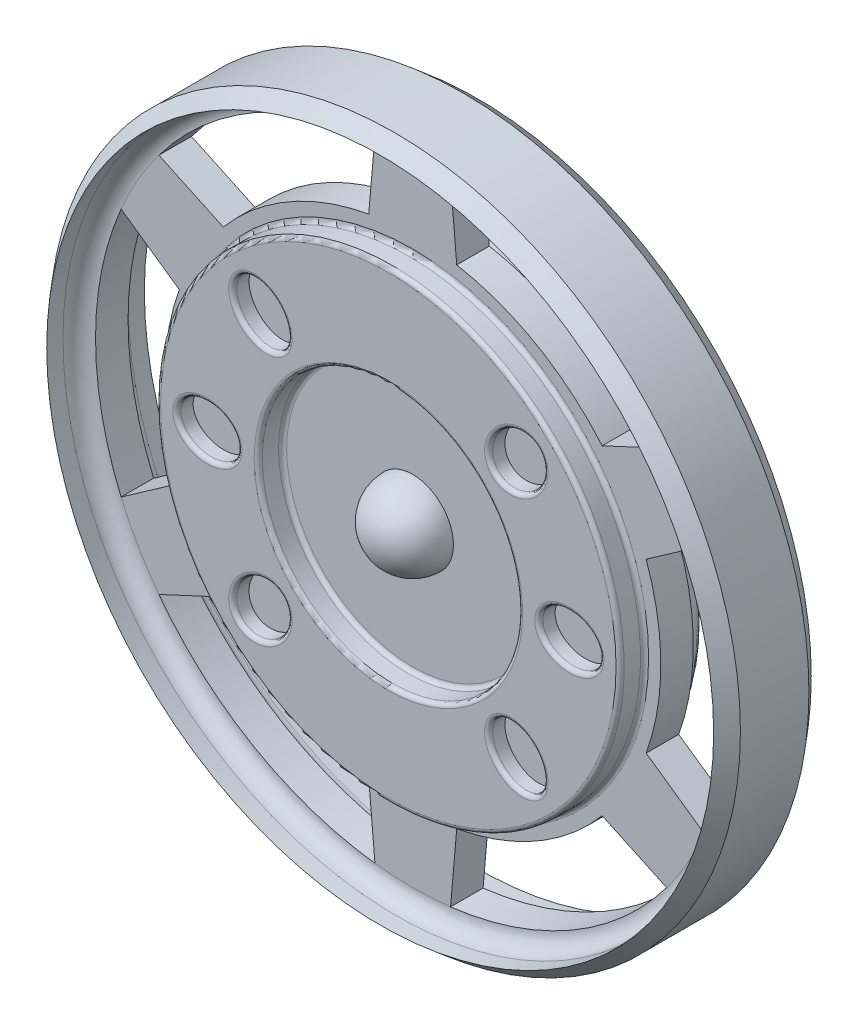
SolidWorks part; units mm, degrees
material "AISI 1020"
ref_plane "Front Plane" through (0, 0, 0) normal (0, 0, 1) x (1, 0, 0)
ref_plane "Top Plane" through (0, 0, 0) normal (0, 1, 0) x (1, 0, 0)
ref_plane "Right Plane" through (0, 0, 0) normal (1, 0, 0) x (0, 0, -1)
sketch "Sketch1" plane through (0, 0, 0) normal (1, 0, 0) x (0, 0, -1)
  line L0 (0, 0) -> (0, 107.95) construction
  line L1 (10.6994, 107.95) -> (-10.6994, 107.95)
  line L2 (-10.6994, 107.95) -> (-15.24, 104.14)
  line L3 (-15.24, 104.14) -> (-10.16, 104.14)
  line L4 (-5.08, 99.06) -> (-5.08, 72.39)
  line L5 (-5.08, 72.39) -> (-12.7, 72.39)
  line L6 (-12.7, 72.39) -> (-12.7, 40.64)
  line L7 (-12.7, 40.64) -> (-5.08, 40.64)
  line L8 (-5.08, 40.64) -> (-5.08, 12.7)
  line L9 (-17.78, 0) -> (17.78, 0)
  line L10 (5.08, 40.64) -> (5.08, 12.7)
  line L11 (12.7, 40.64) -> (5.08, 40.64)
  line L12 (12.7, 72.39) -> (12.7, 40.64)
  line L13 (5.08, 72.39) -> (12.7, 72.39)
  line L14 (5.08, 99.06) -> (5.08, 72.39)
  line L15 (15.24, 104.14) -> (10.16, 104.14)
  line L16 (10.6994, 107.95) -> (15.24, 104.14)
  arc A0 (-10.16, 104.14) -> (-5.08, 99.06) centre (-10.16, 99.06) cw
  arc A1 (-5.08, 12.7) -> (-17.78, 0) centre (-5.08, 0) ccw
  arc A2 (5.08, 12.7) -> (17.78, 0) centre (5.08, 0) cw
  arc A3 (10.16, 104.14) -> (5.08, 99.06) centre (10.16, 99.06) ccw
  point P22 (0, 0)
revolve "Base" add sketch "Sketch1" angle 360 about L9
sketch "Sketch2" plane through (0, 0, 5.08) normal (0, 0, 1) x (1, 0, 0)
  line L0 (0, 0) -> (-99.06, 0) construction
  line L1 (-91.0806, -38.9515) -> (-72.898, -26.2199)
  line L2 (-91.0806, 38.9515) -> (-72.898, 26.2199)
  circle A0 centre (0, 0) radius 99.06 construction
  arc A1 (-91.0806, 38.9515) -> (-91.0806, -38.9515) centre (0, 0) ccw
  circle A4 centre (0, 0) radius 77.47
  arc A5 (-72.898, 26.2199) -> (-72.898, -26.2199) centre (0, 0) ccw
extrude "Outer Cuts" cut sketch "Sketch2" against normal through all both and the other way through all
pattern_circular "Outer Cut CirPattern1" count 6 over 360 about axis through (0, 0, 0) along (0, 0, 1) of "Outer Cuts"
sketch "Sketch3" plane through (0, 0, 12.7) normal (0, 0, 1) x (1, 0, 0)
  line L0 (-40.64, 0) -> (-72.39, 0) construction
  line L1 (0, 0) -> (-39.9621, 39.9621) construction
  circle A0 centre (0, 0) radius 56.515 construction
  circle A1 centre (0, 0) radius 40.64 construction
  circle A2 centre (0, 0) radius 40.64 construction
  circle A3 centre (0, 0) radius 72.39 construction
  ellipse E0 centre (-39.9621, 39.9621) end of major axis (-33.2269, 33.2269) minor radius 7.62
  point P12 (-56.515, 0)
extrude "Circle Cuts" cut sketch "Sketch3" against normal offset from surface (5.08 mm away) 2.54 up to face at (12.7, 0, 5.08)
pattern_circular "Circle Cut CirPattern2" count 8 over 360 about axis through (0, 0, 5.08) along (0, 0, 1) skipping 3, 7 of "Circle Cuts"
mirror "Mirror1" about plane through (0, 0, 0) normal (0, 0, 1) of "Circle Cut CirPattern2", "Circle Cuts"
fillet "Fillet3" radius 1.27 20 edges at (72.39, 0, 5.08) (72.39, 0, 12.7) (40.64, 0, 12.7) (40.64, 0, 5.08) (-33.2269, 33.2269, 12.7) (40.64, 0, -5.08) (33.2269, 33.2269, 12.7) (46.99, 0, 12.7) (33.2269, -33.2269, 12.7) (40.64, 0, -12.7) (-33.2269, -33.2269, 12.7) (-46.99, 0, 12.7) (72.39, 0, -12.7) (72.39, 0, -5.08) (33.2269, 33.2269, -12.7) (46.99, 0, -12.7) (33.2269, -33.2269, -12.7) (-33.2269, -33.2269, -12.7) (-46.99, 0, -12.7) (-33.2269, 33.2269, -12.7)
equation "\"A\"= 4.25"
equation "\"B\"= 1.00"
equation "\"C\"= 70"
equation "\"D\"= 2.87"
equation "\"E\"= 45"
equation "\"F\"= 0.75"
equation "\"D1@Sketch1\"=\"A\""
equation "\"D2@Sketch1\"=\"B\""
equation "\"D2@Sketch2\"=\"C\""
equation "\"D3@Sketch2\"=\"D\""
equation "\"D1@Sketch3\"=\"E\""
equation "\"D3@Sketch3\"=\"F\""
